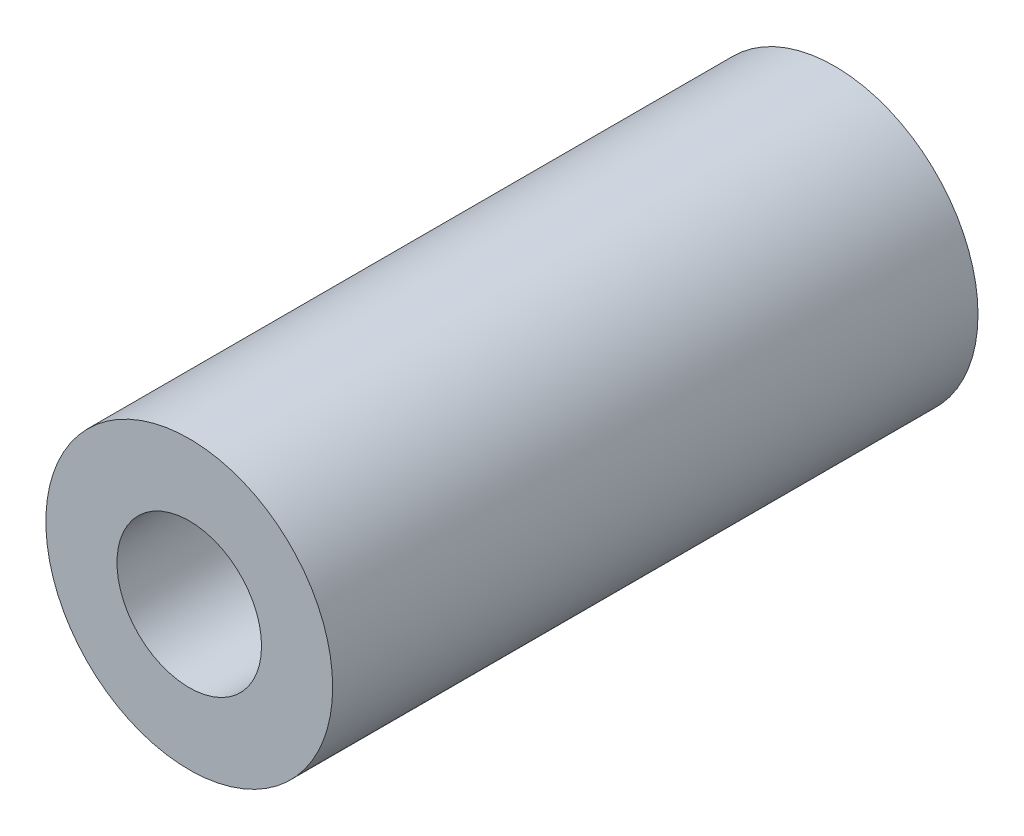
SolidWorks part; units mm, degrees
ref_plane "Front Plane" through (0, 0, 0) normal (0, 0, 1) x (1, 0, 0)
ref_plane "Top Plane" through (0, 0, 0) normal (0, 1, 0) x (1, 0, 0)
ref_plane "Right Plane" through (0, 0, 0) normal (1, 0, 0) x (0, 0, -1)
sketch "Sketch1" plane through (0, 0, 0) normal (0, 0, 1) x (1, 0, 0)
  circle A0 centre (0, 0) radius 6.35
  circle A1 centre (0, 0) radius 3.2004
  dimension "OD" = 12.7
  dimension "ID" = 6.4008
extrude "Extrude1" add sketch "Sketch1" along normal mid plane 28.575
sketch "Sketch2" plane through (0, 0, 0) normal (1, 0, 0) x (0, 0, -1)
  line L0 (-14.2875, -3.2004) -> (14.2875, -3.2004) construction
  line L3 (14.2875, 3.2004) -> (-14.2875, 3.2004) construction
  line L5 (-14.2875, -3.2004) -> (14.2875, -3.2004)
  line L6 (14.2875, 3.2004) -> (-14.2875, 3.2004)
sketch "Sketch4" plane through (0, 0, 14.2875) normal (0, 0, 1) x (1, 0, 0)
  line L0 (0, 0) -> (-2.263, 2.263)
  line L1 (0, -5.2388) -> (0, 5.2388) construction
  circle A0 centre (0, 0) radius 3.2004 construction
  dimension "D1" = 45
